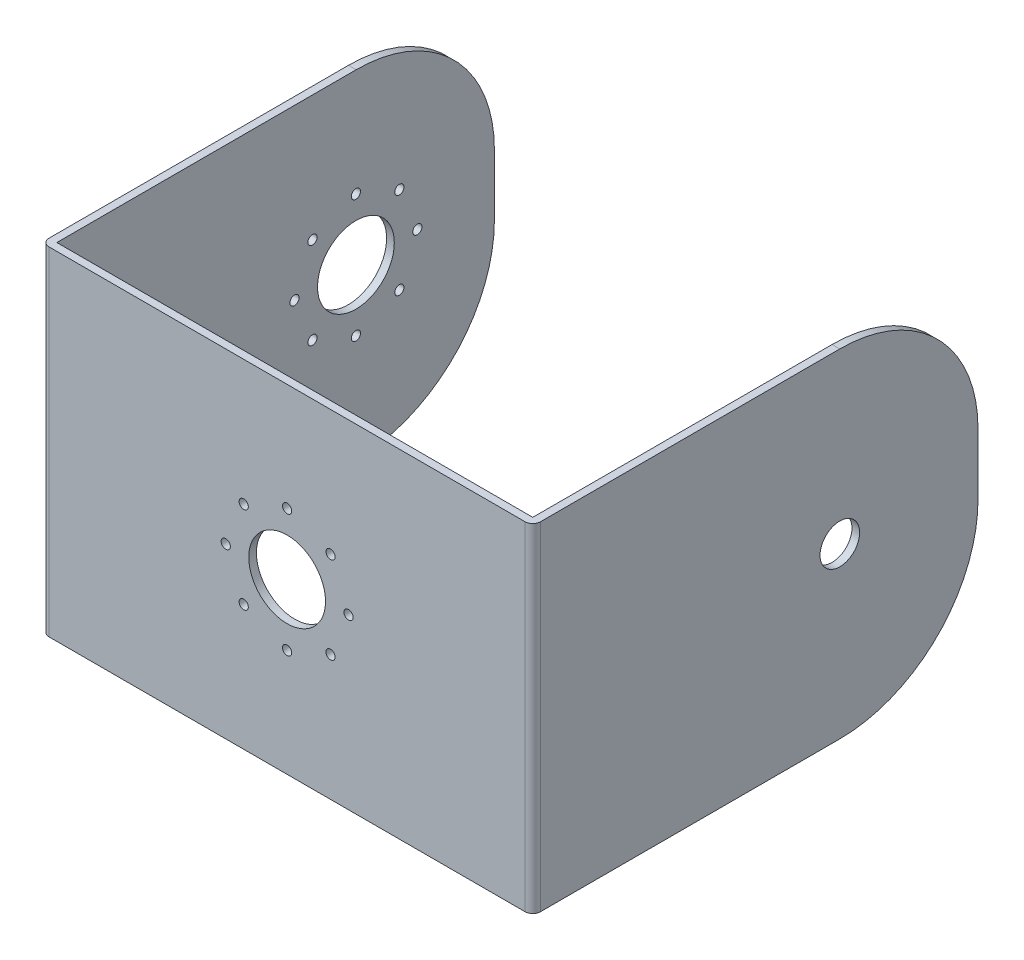
SolidWorks part; units mm, degrees
ref_plane "Front Plane" through (0, 0, 0) normal (0, 0, 1) x (1, 0, 0)
ref_plane "Top Plane" through (0, 0, 0) normal (0, 1, 0) x (1, 0, 0)
ref_plane "Right Plane" through (0, 0, 0) normal (1, 0, 0) x (0, 0, -1)
sketch "Sketch1" plane through (0, 0, 0) normal (0, 1, 0) x (1, 0, 0)
  line L0 (31, 0) -> (-31, 0)
  line L1 (-31, 0) -> (-31, 57)
  line L2 (31, 0) -> (31, 57)
  point P4 (0, 0)
extrude "Extrude-Thin1" add sketch "Sketch1" along normal blind 44 thin thin type one direction wall 1
sketch "Sketch2" plane through (32, 0, 0) normal (1, 0, 0) x (0, 0, -1)
  circle A0 centre (39, 22) radius 2.58
extrude "Cut-Extrude1" cut sketch "Sketch2" against normal blind 10
fillet "Fillet1" radius 18 1 edges at (31.5, 0, -57)
fillet "Fillet2" radius 18 1 edges at (31.5, 44, -57)
fillet "Fillet3" radius 18 1 edges at (-31.5, 44, -57)
fillet "Fillet4" radius 18 1 edges at (-31.5, 0, -57)
fillet "Fillet5" radius 1 1 edges at (-32, 22, 1)
fillet "Fillet6" radius 1 1 edges at (32, 22, 1)
sketch "Sketch11" plane through (-32, 0, 0) normal (-1, 0, 0) x (0, 0, 1)
  circle A0 centre (-38.961, 22) radius 5
  circle A2 centre (-38.961, 30) radius 0.6
  circle A3 centre (-30.961, 22) radius 0.6
  circle A4 centre (-38.961, 14) radius 0.6
  circle A5 centre (-46.961, 22) radius 0.6
  circle A6 centre (-44.6179, 27.6569) radius 0.6
  circle A7 centre (-33.3041, 27.6569) radius 0.6
  circle A8 centre (-33.3041, 16.3431) radius 0.6
  circle A9 centre (-44.6179, 16.3431) radius 0.6
extrude "Cut-Extrude2" cut sketch "Sketch11" against normal blind 10
sketch "Sketch12" plane through (0, 0, 1) normal (0, 0, 1) x (1, 0, 0)
  circle A0 centre (0, 22) radius 5
  circle A2 centre (0, 30) radius 0.6
  circle A3 centre (5.6569, 27.6569) radius 0.6
  circle A4 centre (8, 22) radius 0.6
  circle A5 centre (5.6569, 16.3431) radius 0.6
  circle A6 centre (0, 14) radius 0.6
  circle A7 centre (-5.6569, 16.3431) radius 0.6
  circle A8 centre (-8, 22) radius 0.6
  circle A9 centre (-5.6569, 27.6569) radius 0.6
extrude "Cut-Extrude3" cut sketch "Sketch12" against normal blind 10
